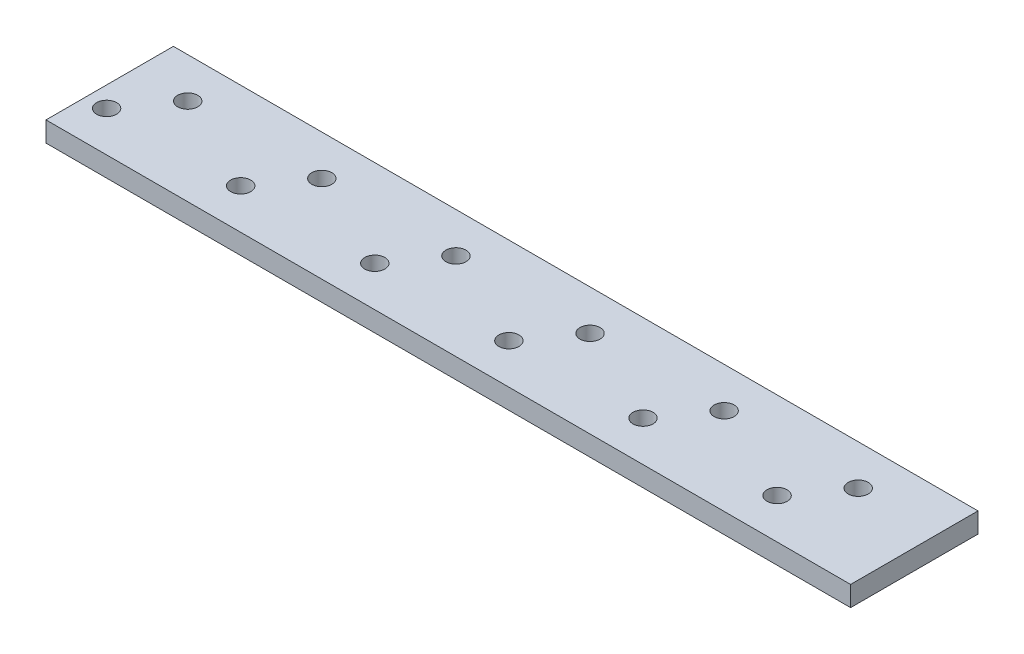
SolidWorks part; units mm, degrees
ref_plane "Спереди" through (0, 0, 0) normal (0, 0, 1) x (1, 0, 0)
ref_plane "Сверху" through (0, 0, 0) normal (0, 1, 0) x (1, 0, 0)
ref_plane "Справа" through (0, 0, 0) normal (1, 0, 0) x (0, 0, -1)
other "Configuration Table"
sketch "Эскиз1" plane through (0, 0, 0) normal (0, 1, 0) x (1, 0, 0)
  line L1 (-60, -9.5) -> (60, -9.5)
  line L2 (-60, -9.5) -> (-60, 9.5)
  line L3 (-60, 9.5) -> (60, 9.5)
  line L4 (60, -9.5) -> (60, 9.5)
  line L5 (0, 9.5) -> (0, -9.5) construction
  line L6 (-60, 0) -> (60, 0) construction
  point P0 (0, 0)
  dimension "D1" = 120
  dimension "D2" = 19
extrude "Бобышка-Вытянуть1" add sketch "Эскиз1" along normal blind 3
sketch "Эскиз2" plane through (0, 3, 0) normal (0, 1, 0) x (1, 0, 0)
  line L0 (-60, 3.5) -> (60, 3.5) construction
  line L1 (-60, 9.5) -> (-60, -9.5) construction
  line L2 (60, -9.5) -> (60, 9.5) construction
  line L3 (-60, -3.5) -> (60, -3.5) construction
  line L4 (60, 9.5) -> (-60, 9.5) construction
  line L5 (-60, -9.5) -> (60, -9.5) construction
  circle A0 centre (-51.8624, 3.5) radius 1.5
  circle A1 centre (-56.9637, -3.5) radius 1.5
  circle A2 centre (-31.8624, 3.5) radius 1.5
  circle A3 centre (-36.9637, -3.5) radius 1.5
  circle A4 centre (-11.8624, 3.5) radius 1.5
  circle A5 centre (-16.9637, -3.5) radius 1.5
  circle A6 centre (8.1376, 3.5) radius 1.5
  circle A7 centre (3.0363, -3.5) radius 1.5
  circle A8 centre (28.1376, 3.5) radius 1.5
  circle A9 centre (23.0363, -3.5) radius 1.5
  circle A10 centre (48.1376, 3.5) radius 1.5
  circle A11 centre (43.0363, -3.5) radius 1.5
  dimension "D3" = 6
  dimension "D1" = 6
  dimension "D2" = 6
extrude "Вырез-Вытянуть1" cut sketch "Эскиз2" against normal blind 3
